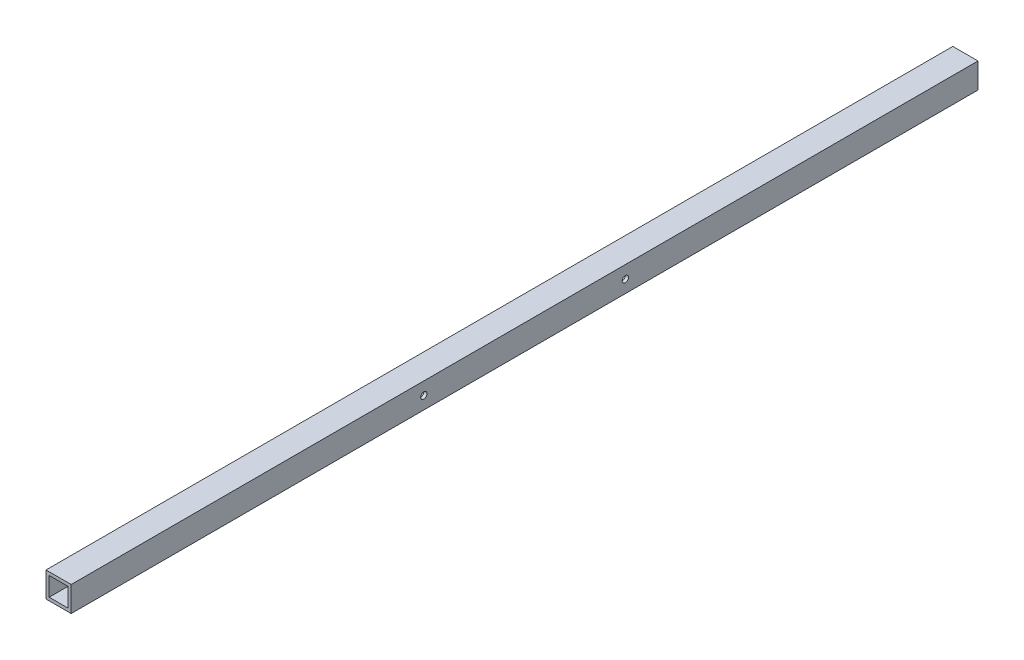
SolidWorks part; units mm, degrees
ref_plane "Front Plane" through (0, 0, 0) normal (0, 0, 1) x (1, 0, 0)
ref_plane "Top Plane" through (0, 0, 0) normal (0, 1, 0) x (1, 0, 0)
ref_plane "Right Plane" through (0, 0, 0) normal (1, 0, 0) x (0, 0, -1)
sketch "Sketch1" plane through (0, 0, 0) normal (0, 0, 1) x (1, 0, 0)
  line L1 (-9.525, 9.525) -> (9.525, 9.525)
  line L2 (-9.525, 9.525) -> (-9.525, -9.525)
  line L3 (-9.525, -9.525) -> (9.525, -9.525)
  line L4 (9.525, 9.525) -> (9.525, -9.525)
  line L5 (-9.525, 9.525) -> (9.525, -9.525) construction
  line L6 (-9.525, -9.525) -> (9.525, 9.525) construction
  line L7 (-12.7, 12.7) -> (12.7, 12.7)
  line L8 (-12.7, 12.7) -> (-12.7, -12.7)
  line L9 (-12.7, -12.7) -> (12.7, -12.7)
  line L10 (12.7, 12.7) -> (12.7, -12.7)
  line L11 (-12.7, 12.7) -> (12.7, -12.7) construction
  line L12 (-12.7, -12.7) -> (12.7, 12.7) construction
  point P0 (0, 0)
  point P6 (0, 0)
  dimension "D1" = 25.4
  dimension "D2" = 3.175
  dimension "D3" = 25.4
extrude "Boss-Extrude1" add sketch "Sketch1" along normal blind 914.4
sketch "Sketch2" plane through (12.7, 0, 0) normal (1, 0, 0) x (0, 0, -1)
  line L0 (-457.2, 12.7) -> (-457.2, -12.7) construction
  line L1 (-914.4, 12.7) -> (0, 12.7) construction
  line L2 (-914.4, -12.7) -> (0, -12.7) construction
  line L3 (-457.2, 0) -> (-558.8, 0) construction
  circle A0 centre (-558.8, 0) radius 3.175
  circle A1 centre (-355.6, 0) radius 3.175
  dimension "D2" = 6.35
  dimension "D1" = 101.6
extrude "Cut-Extrude1" cut sketch "Sketch2" against normal through all
